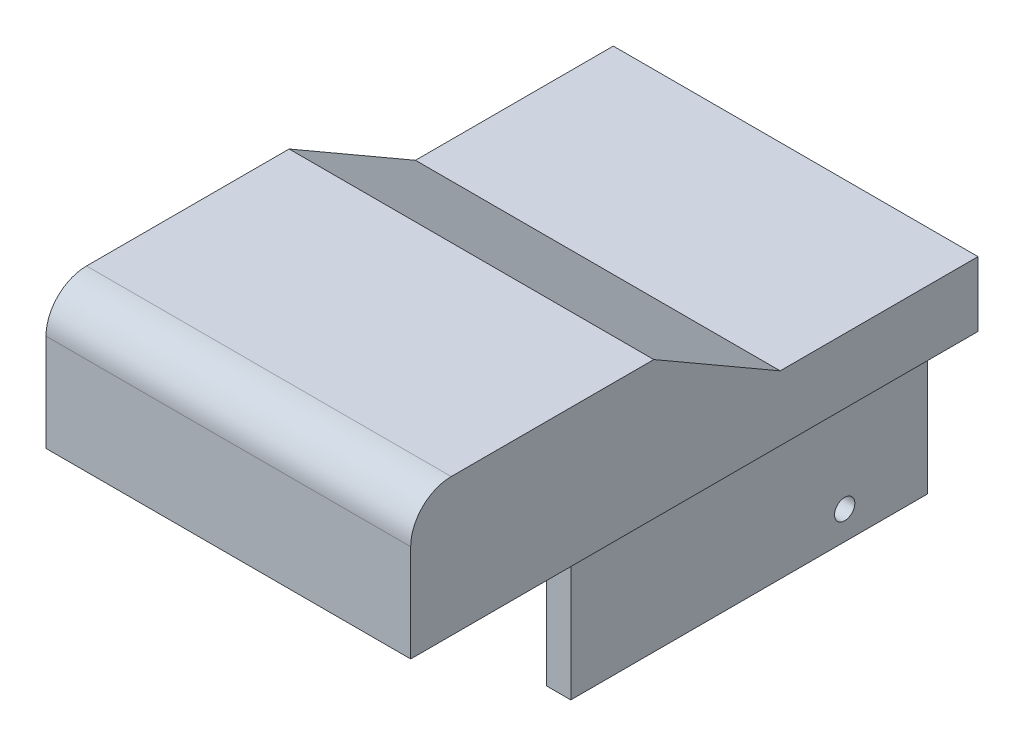
SolidWorks part; units mm, degrees
ref_plane "Front Plane" through (0, 0, 0) normal (0, 0, 1) x (1, 0, 0)
ref_plane "Top Plane" through (0, 0, 0) normal (0, 1, 0) x (1, 0, 0)
ref_plane "Right Plane" through (0, 0, 0) normal (1, 0, 0) x (0, 0, -1)
sketch "Sketch1" plane through (0, 0, 0) normal (1, 0, 0) x (0, 0, -1)
  line L0 (5, 0) -> (30, 0)
  line L1 (30, 0) -> (45.5885, -9)
  line L2 (63.3185, -17) -> (0, -17)
  line L3 (0, -17) -> (0, -5)
  line L4 (63.3185, -17) -> (70, -17)
  line L5 (70, -17) -> (70, -9)
  line L6 (70, -9) -> (45.5885, -9)
  arc A0 (5, 0) -> (0, -5) centre (5, -5) ccw
  point P7 (0, 0)
  dimension "D4" = 5
  dimension "D1" = 17
  dimension "D2" = 30
  dimension "D3" = 150
  dimension "D5" = 8
  dimension "D6" = 70
extrude "Boss-Extrude1" add sketch "Sketch1" along normal mid plane 45
sketch "Sketch2" plane through (0, -17, 0) normal (0, -1, 0) x (1, 0, 0)
  line L0 (0, 0) -> (0, -70) construction
  line L1 (13.25, -70) -> (16.25, -70)
  line L2 (13.25, -70) -> (13.25, -26)
  line L3 (13.25, -26) -> (16.25, -26)
  line L4 (16.25, -70) -> (16.25, -26)
  line L5 (22.5, -70) -> (-22.5, -70) construction
  line L6 (-16.25, -70) -> (-16.25, -26)
  line L7 (-13.25, -26) -> (-16.25, -26)
  line L8 (-13.25, -70) -> (-13.25, -26)
  line L9 (-13.25, -70) -> (-16.25, -70)
  dimension "D1" = 3
  dimension "D2" = 44
  dimension "D3" = 13.25
extrude "Boss-Extrude2" add sketch "Sketch2" along normal blind 20.5
sketch "Sketch3" plane through (-16.25, 0, 0) normal (-1, 0, 0) x (0, 0, 1)
  line L0 (-70, -37.5) -> (-70, -17) construction
  line L1 (-26, -37.5) -> (-70, -37.5) construction
  line L2 (0, -17) -> (-70, -17) construction
  circle A0 centre (-59.8, -34) radius 1.25
  circle A1 centre (-39.5, -20.5) radius 1.25
  dimension "D1" = 2.5
  dimension "D4" = 2.5
  dimension "D2" = 10.2
  dimension "D3" = 3.5
  dimension "D5" = 30.5
  dimension "D6" = 3.5
extrude "Cut-Extrude1" cut sketch "Sketch3" against normal through all
